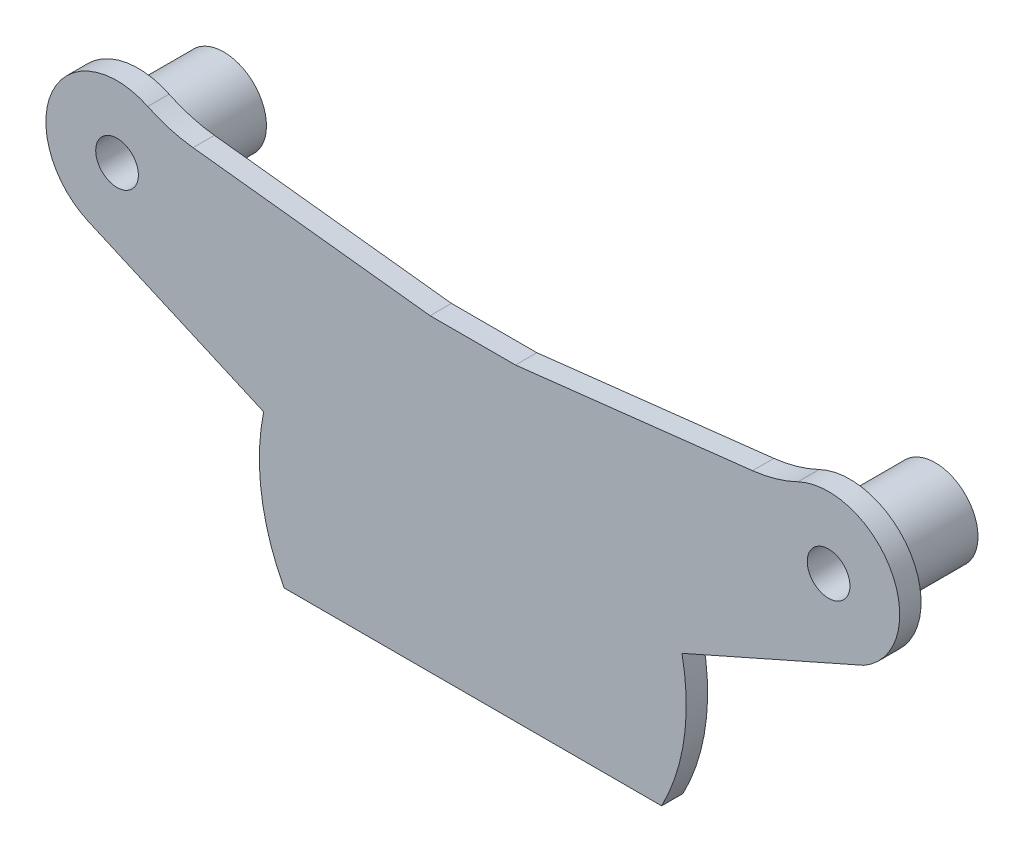
SolidWorks part; units mm, degrees
ref_plane "Спереди" through (0, 0, 0) normal (0, 0, 1) x (1, 0, 0)
ref_plane "Сверху" through (0, 0, 0) normal (0, 1, 0) x (1, 0, 0)
ref_plane "Справа" through (0, 0, 0) normal (1, 0, 0) x (0, 0, -1)
other "Configuration Table"
sketch "Эскиз1" plane through (0, 0, 0) normal (0, 0, 1) x (1, 0, 0)
  line L3 (-13.2665, -7) -> (13.2665, -7)
  line L8 (0, 0) -> (0, 8.6282) construction
  line L9 (3, 14.6969) -> (19.6571, 16.5948) construction
  line L37 (-19.6571, 16.5948) -> (-3, 14.6969) construction
  line L38 (3, 14.6969) -> (19.6571, 16.5948)
  line L39 (-14.6969, 3) -> (-27.015, 8.424)
  line L40 (14.6969, 3) -> (27.4936, 8.6662)
  line L41 (-19.6571, 16.5948) -> (-3, 14.6969)
  line L42 (-3, 14.6969) -> (3, 14.6969)
  circle A3 centre (-25, 13) radius 1.5
  circle A4 centre (25, 13) radius 1.5
  arc A12 (-22.8417, 17.5102) -> (-27.015, 8.424) centre (-25, 13) ccw
  arc A13 (27.4936, 8.6662) -> (22.8417, 17.5102) centre (25, 13) ccw
  arc A16 (-14.6969, 3) -> (14.6969, 3) centre (0, 0) ccw
  arc A19 (19.6571, 16.5948) -> (22.8417, 17.5102) centre (18.525, 26.5305) ccw construction
  arc A20 (-22.8417, 17.5102) -> (-19.6571, 16.5948) centre (-18.525, 26.5305) ccw construction
  arc A21 (19.6571, 16.5948) -> (22.8417, 17.5102) centre (18.525, 26.5305) ccw
  arc A22 (-22.8417, 17.5102) -> (-19.6571, 16.5948) centre (-18.525, 26.5305) ccw
  dimension "D1" = 30
  dimension "D4" = 3
  dimension "D6" = 3
  dimension "D2" = 7
  dimension "D3" = 13
  dimension "D5" = 50
extrude "Бобышка-Вытянуть1" add sketch "Эскиз1" along normal blind 1.5
sketch "Эскиз4" plane through (0, 0, 0) normal (0, 0, -1) x (-1, 0, 0)
  line L0 (0, 0) -> (0, 21.2157) construction
  circle A0 centre (25, 13) radius 3
  circle A1 centre (25, 13) radius 1.5
  circle A2 centre (-25, 13) radius 1.5
  circle A3 centre (-25, 13) radius 3
  dimension "D1" = 6
extrude "Бобышка-Вытянуть2" add sketch "Эскиз4" along normal blind 6
fillet "Скругление1" radius 1 2 edges at (-22, 13, 0) (28, 13, 0)
